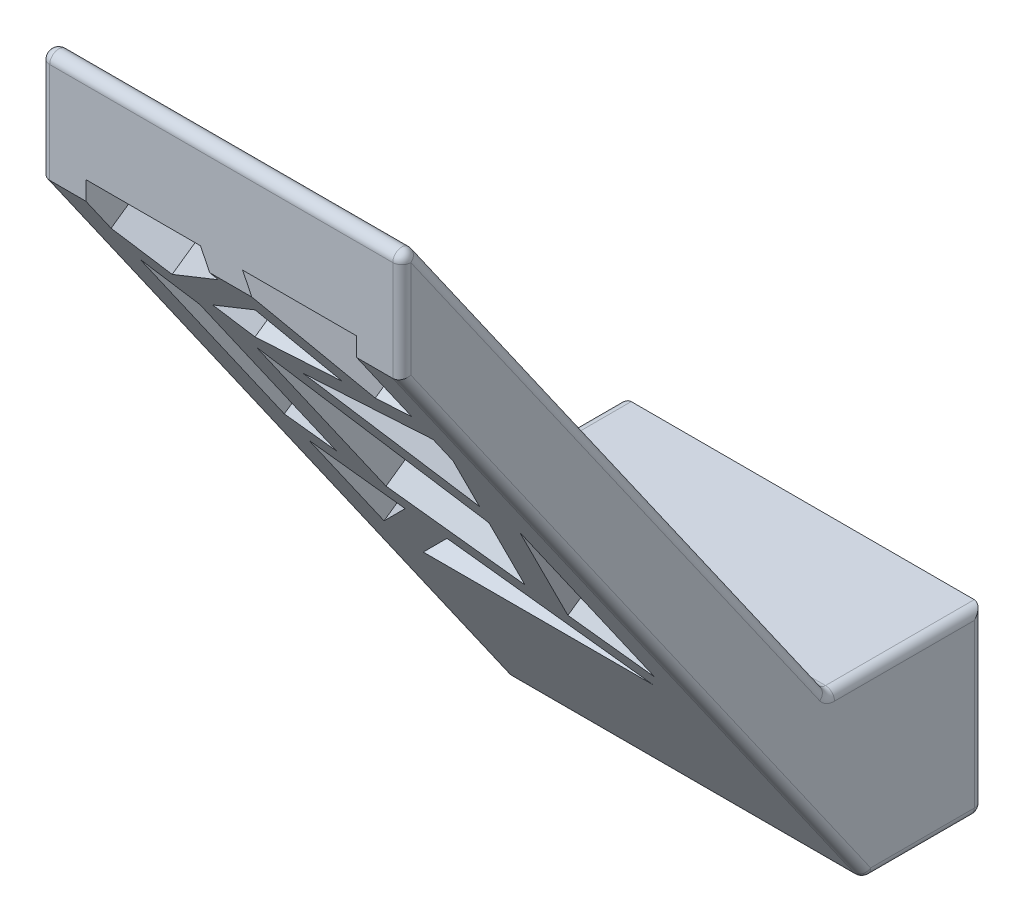
SolidWorks part; units mm, degrees
ref_plane "Front Plane" through (0, 0, 0) normal (0, 0, 1) x (1, 0, 0)
ref_plane "Top Plane" through (0, 0, 0) normal (0, 1, 0) x (1, 0, 0)
ref_plane "Right Plane" through (0, 0, 0) normal (1, 0, 0) x (0, 0, -1)
sketch "Sketch1" plane through (0, 0, 0) normal (0, 0, 1) x (1, 0, 0)
  line L1 (-73, 11.5) -> (-93, 11.5)
  line L2 (-73, 11.5) -> (-73, 21.5)
  line L3 (-73, 21.5) -> (-93, 21.5)
  line L4 (-93, 11.5) -> (-93, 21.5)
extrude "Boss-Extrude1" add sketch "Sketch1" along normal blind 5
sketch "Sketch2" plane through (-93, 0, 0) normal (-1, 0, 0) x (0, 0, 1)
  line L0 (0, 16.5) -> (5, 16.5) construction
  line L1 (0, 21.5) -> (0, 11.5) construction
  line L2 (5, 21.5) -> (5, 11.5) construction
  line L3 (5, 16.5) -> (1.499, 11.5)
  line L4 (5, 11.5) -> (0, 11.5) construction
  line L5 (1.499, 11.5) -> (6.499, 11.5)
  line L6 (6.499, 11.5) -> (32.2081, 48.2164)
  line L7 (8.501, 21.5) -> (32.2081, 55.3571)
  line L9 (32.2081, 55.3571) -> (32.2081, 48.2164)
  line L10 (5, 21.5) -> (8.501, 21.5)
  line L12 (5, 16.5) -> (5, 21.5)
  dimension "D1" = 35
  dimension "D2" = 5
extrude "Boss-Extrude2" add sketch "Sketch2" against normal up to surface (20 mm away) up to face at (-73, 16.5, 2.5)
sketch "Sketch3" plane through (0, 3.0791, -4.3974) normal (0, 0.5736, -0.8192) x (-1, 0, 0)
  line L0 (93, 58.8197) -> (73, 58.8197)
  line L1 (93, 63.8197) -> (93, 22.4878) construction
  line L2 (73, 22.4878) -> (73, 63.8197) construction
  line L3 (75.5, 58.8197) -> (75.5, 27.4878)
  line L4 (75.5, 27.4878) -> (90.5, 27.4878)
  line L5 (90.5, 27.4878) -> (90.5, 58.8197)
  line L6 (73, 63.8197) -> (93, 63.8197) construction
  line L7 (73, 22.4878) -> (93, 22.4878) construction
  line L8 (90.5, 38.8025) -> (88.3831, 37.4432)
  line L10 (76.5806, 27.4878) -> (84.9126, 32.8379)
  line L11 (90.5, 36.4257) -> (90.5, 38.8025)
  line L12 (80.76, 32.5482) -> (78.13, 40.6087)
  line L13 (75.5, 48.6691) -> (75.5, 42.2215)
  line L14 (75.5, 42.2215) -> (79.0207, 31.4314)
  line L16 (78.13, 40.6087) -> (86.3831, 48.6959)
  line L17 (90.5, 52.7301) -> (90.5, 55.5303)
  line L18 (90.5, 55.5303) -> (88.3347, 53.4085)
  line L20 (88.3831, 50.6557) -> (88.3831, 37.4432)
  line L22 (86.3831, 36.1589) -> (86.3831, 48.6959)
  line L24 (85.3975, 50.5303) -> (79.8807, 51.703)
  line L25 (75.5, 52.6342) -> (75.5, 50.5895)
  line L26 (75.5, 50.5895) -> (83.6828, 48.8501)
  line L28 (79.8807, 51.703) -> (82.3534, 55.8263)
  line L29 (84.1484, 58.8197) -> (81.8164, 58.8197)
  line L30 (81.8164, 58.8197) -> (77.8124, 52.1426)
  line L32 (83.3951, 57.5635) -> (88.3347, 53.4085)
  line L34 (86.8996, 52.0022) -> (82.3534, 55.8263)
  line L36 (75.5, 29.1707) -> (75.5, 27.4878)
  line L37 (76.5806, 27.4878) -> (75.5, 27.4878)
  line L38 (75.5, 27.4878) -> (75.5, 29.1707)
  line L39 (75.5, 27.4878) -> (76.5806, 27.4878)
  line L40 (75.5, 27.4878) -> (75.5, 29.1707)
  line L41 (90.5, 36.4257) -> (90.5, 38.8025)
  line L42 (84.9126, 32.8379) -> (89.293, 27.4878)
  line L43 (89.293, 27.4878) -> (90.5, 27.4878)
  line L44 (90.5, 29.1707) -> (86.6068, 33.9258)
  line L46 (90.5, 29.1707) -> (90.5, 27.4878)
  line L47 (76.5806, 27.4878) -> (75.5, 27.4878)
  line L48 (75.5, 29.1707) -> (75.5, 27.4878)
  line L49 (90.5, 36.4257) -> (90.5, 38.8025)
  line L50 (86.6068, 33.9258) -> (90.5, 36.4257)
  line L51 (79.0207, 31.4314) -> (75.5, 29.1707)
  line L52 (86.3831, 36.1589) -> (80.76, 32.5482)
  line L53 (77.4377, 42.7304) -> (75.5, 48.6691)
  line L54 (83.6828, 48.8501) -> (77.4377, 42.7304)
  line L55 (86.8996, 52.0022) -> (85.3975, 50.5303)
  line L56 (77.8124, 52.1426) -> (75.5, 52.6342)
  line L57 (83.3951, 57.5635) -> (84.1484, 58.8197)
  line L58 (88.3831, 50.6557) -> (90.5, 52.7301)
  point P42 (88.3831, 44.0495)
  dimension "D1" = 2.5
  dimension "D2" = 2.5
  dimension "D3" = 5
  dimension "D4" = 5
  dimension "D5" = 2
  dimension "D6" = 2
  dimension "D7" = 2
  dimension "D8" = 2
  dimension "D9" = 2
  dimension "D10" = 2
  dimension "D11" = 2
  dimension "D12" = 2
extrude "Cut-Extrude1" cut sketch "Sketch3" against normal up to surface (4.0958 mm away) contours L50 L44 L5 | L42 L10 L4 | L51 L14 L3 | L54 L26 L3 L53 | L56 L30 L0 L3 | L57 L32 L18 L5 L0 | L55 L34 L28 L24 | L58 L20 L8 L5 | L52 L22 L16 L12 up to face at (-83, 29.8582, 19.3535)
fillet "Fillet1" radius 0.5 50 edges at (-93, 21.5, 4.2505) (-73, 21.5, 4.2505) (-75.5, 43.733, 24.0688) (-76.4689, 40.5142, 21.8149) (-80.5603, 40.5883, 21.8668) (-79.5914, 43.8072, 24.1207) (-78.6582, 51.2614, 29.3402) (-75.5, 48.7279, 27.5662) (-76.6562, 45.9932, 25.6513) (-79.8144, 48.5266, 27.4253) (-82.9368, 25.5958, 11.3689) (-87.1028, 27.7871, 12.9033) (-80.7466, 27.7871, 12.9033) (-75.5, 32.3196, 16.077) (-77.2603, 27.9003, 12.9825) (-77.2603, 33.2455, 16.7254) (-90.5, 29.9458, 14.4148) (-88.5534, 31.8934, 15.7785) (-88.5534, 28.9219, 13.6979) (-83, 55.3571, 32.2081) (-73, 38.4286, 20.3545) (-93, 38.4286, 20.3545) (-83, 21.5, 8.501) (-81.1171, 47.1205, 26.4407) (-82.6391, 44.9514, 24.9219) (-86.1485, 45.0739, 25.0077) (-84.6265, 47.2431, 26.5265) (-89.4173, 47.6978, 26.8449) (-90.5, 49.9141, 28.3968) (-87.3242, 51.2614, 29.3402) (-83.7718, 50.7469, 28.9799) (-85.8649, 48.5306, 27.428) (-89.4415, 34.3075, 17.4689) (-90.5, 40.5687, 21.8531) (-89.4415, 45.4235, 25.2524) (-88.3831, 39.1623, 20.8683) (-82.2565, 39.6561, 21.2141) (-79.445, 33.0424, 16.5831) (-83.5715, 31.2199, 15.307) (-86.3831, 37.8336, 19.938) (-83, 11.5, 6.499) (-83, 11.5, 0) (-73, 51.7868, 32.2081) (-93, 51.7868, 32.2081) (-73, 16.5, 0) (-93, 29.8582, 19.3535) (-73, 29.8582, 19.3535) (-93, 11.5, 3.2495) (-93, 16.5, 0) (-73, 11.5, 3.2495)
